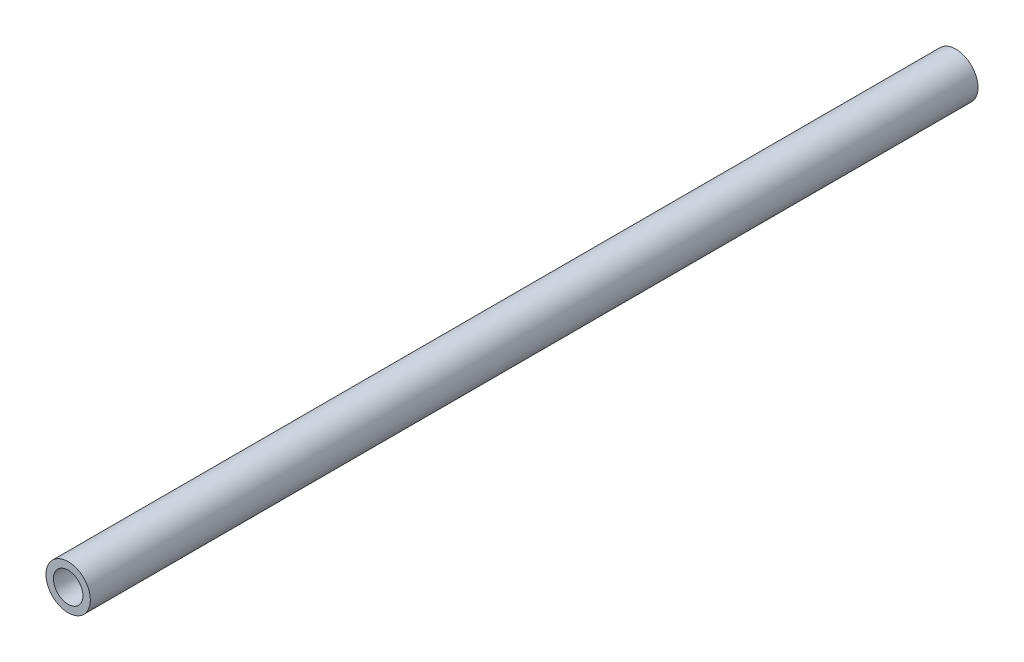
SolidWorks part; units mm, degrees
material "PVC Rigid"
ref_plane "Front Plane" through (0, 0, 0) normal (0, 0, 1) x (1, 0, 0)
ref_plane "Top Plane" through (0, 0, 0) normal (0, 1, 0) x (1, 0, 0)
ref_plane "Right Plane" through (0, 0, 0) normal (1, 0, 0) x (0, 0, -1)
sketch "Sketch1" plane through (0, 0, 0) normal (0, 0, 1) x (1, 0, 0)
  circle A0 centre (0, 0) radius 7.62
  circle A2 centre (0, 0) radius 5.08
  dimension "D1" = 15.24
  dimension "D2" = 10.16
extrude "Boss-Extrude1" add sketch "Sketch1" along normal blind 304.8
